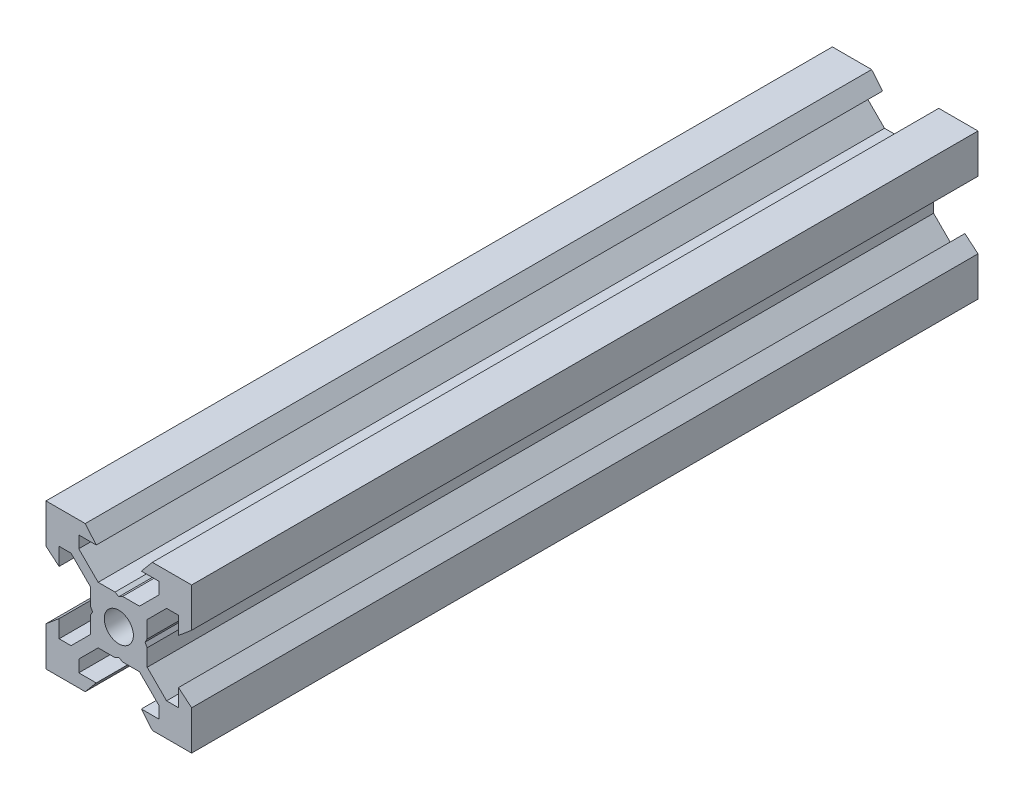
SolidWorks part; units mm, degrees
ref_plane "Front Plane" through (0, 0, 0) normal (0, 0, 1) x (1, 0, 0)
ref_plane "Top Plane" through (0, 0, 0) normal (0, 1, 0) x (1, 0, 0)
ref_plane "Right Plane" through (0, 0, 0) normal (1, 0, 0) x (0, 0, -1)
sketch "Sketch1" plane through (0, 0, 0) normal (0, 0, 1) x (1, 0, 0)
  line L0 (10, 10) -> (4.6104, 10) construction
  line L1 (10, 10) -> (10, 4.6104) construction
  line L2 (10, -10) -> (10, -4.6104) construction
  line L3 (10, -10) -> (4.6104, -10) construction
  line L4 (10, 10) -> (10, 4.6104)
  line L5 (6.5607, 5.5) -> (8.2, 5.5)
  line L6 (5.5, 8.2) -> (5.5, 6.5607)
  line L7 (10, 10) -> (4.6104, 10)
  line L8 (10, 10) -> (10, 4.6104)
  line L9 (6.5607, 5.5) -> (3.9, 2.8393)
  line L10 (5.5, 6.5607) -> (2.8393, 3.9)
  line L11 (10, 4.6104) -> (8.2, 3.1)
  line L12 (4.6104, 10) -> (3.1, 8.2)
  line L13 (8.2, 3.1) -> (8.2, 5.5)
  line L14 (3.1, 8.2) -> (5.5, 8.2)
  line L15 (-6.5607, 5.5) -> (-8.2, 5.5)
  line L16 (6.5607, -5.5) -> (8.2, -5.5)
  line L17 (3.1, -8.2) -> (5.5, -8.2)
  line L18 (8.2, -3.1) -> (8.2, -5.5)
  line L19 (4.6104, -10) -> (3.1, -8.2)
  line L20 (10, -4.6104) -> (8.2, -3.1)
  line L21 (0.5196, -3.9) -> (0, -3.6)
  line L22 (0.5196, 3.9) -> (0, 3.6)
  line L23 (3.6, 0) -> (3.9, -0.5196)
  line L24 (3.9, 0.5196) -> (3.6, 0)
  line L25 (3.9, 0.5196) -> (3.9, 2.8393)
  line L26 (2.8393, 3.9) -> (0.5196, 3.9)
  line L27 (3.9, -2.8393) -> (3.9, -0.5196)
  line L28 (2.8393, -3.9) -> (0.5196, -3.9)
  line L29 (5.5, -6.5607) -> (2.8393, -3.9)
  line L30 (6.5607, -5.5) -> (3.9, -2.8393)
  line L31 (10, -10) -> (10, -4.6104)
  line L32 (10, -10) -> (4.6104, -10)
  line L33 (5.5, -8.2) -> (5.5, -6.5607)
  line L34 (-6.5607, -5.5) -> (-8.2, -5.5)
  line L35 (10, -10) -> (10, -4.6104)
  line L36 (0, 0) -> (0, 8.2) construction
  line L37 (-10, -10) -> (-4.6104, -10) construction
  line L38 (-10, -10) -> (-10, -4.6104) construction
  line L39 (-10, 10) -> (-10, 4.6104) construction
  line L40 (-10, 10) -> (-4.6104, 10) construction
  line L41 (-10, -10) -> (-10, -4.6104)
  line L43 (-5.5, -8.2) -> (-5.5, -6.5607)
  line L44 (-10, -10) -> (-4.6104, -10)
  line L45 (-10, -10) -> (-10, -4.6104)
  line L46 (-6.5607, -5.5) -> (-3.9, -2.8393)
  line L47 (-5.5, -6.5607) -> (-2.8393, -3.9)
  line L48 (-2.8393, -3.9) -> (-0.5196, -3.9)
  line L49 (-3.9, -2.8393) -> (-3.9, -0.5196)
  line L50 (-2.8393, 3.9) -> (-0.5196, 3.9)
  line L51 (-3.9, 0.5196) -> (-3.9, 2.8393)
  line L52 (-3.9, 0.5196) -> (-3.6, 0)
  line L53 (-3.6, 0) -> (-3.9, -0.5196)
  line L54 (-0.5196, 3.9) -> (0, 3.6)
  line L55 (-0.5196, -3.9) -> (0, -3.6)
  line L56 (-10, -4.6104) -> (-8.2, -3.1)
  line L57 (-4.6104, -10) -> (-3.1, -8.2)
  line L58 (-8.2, -3.1) -> (-8.2, -5.5)
  line L59 (-3.1, -8.2) -> (-5.5, -8.2)
  line L60 (-10, -10) -> (10, -10) construction
  line L61 (-10, -10) -> (-10, 10) construction
  line L62 (-3.1, 8.2) -> (-5.5, 8.2)
  line L63 (-8.2, 3.1) -> (-8.2, 5.5)
  line L64 (-4.6104, 10) -> (-3.1, 8.2)
  line L65 (-10, 4.6104) -> (-8.2, 3.1)
  line L66 (-5.5, 6.5607) -> (-2.8393, 3.9)
  line L67 (-6.5607, 5.5) -> (-3.9, 2.8393)
  line L68 (-10, 10) -> (-10, 4.6104)
  line L69 (-10, 10) -> (-4.6104, 10)
  line L70 (-5.5, 8.2) -> (-5.5, 6.5607)
  line L71 (-10, 10) -> (10, 10) construction
  line L72 (-10, 10) -> (-10, 4.6104)
  line L73 (10, -10) -> (10, 10) construction
  line L74 (-10, -10) -> (10, 10) construction
  line L75 (-10, 10) -> (10, -10) construction
  circle A0 centre (0, 0) radius 2
  dimension "D7" = 4
  dimension "D1" = 20
  dimension "D2" = 5.3896
  dimension "D3" = 4.5
  dimension "D4" = 50
  dimension "D5" = 1.8
  dimension "D6" = 1.5104
  dimension "D8" = 5.5
  dimension "D9" = 120
  dimension "D10" = 0.3
  dimension "D11" = 2.3197
  dimension "D12" = 7.8
  dimension "D13" = 7.8
  dimension "D14" = 1.5
  dimension "D15" = 2.6607
extrude "Boss-Extrude1" add sketch "Sketch1" along normal mid plane 108 contours L70 L62 L64 L69 L68 L65 L63 L15 L67 L51 L52 L53 L49 L46 L34 L58 L56 L41 L44 L57 L59 L43 L47 L48 L55 L21 L28 L29 L33 L17 L19 L32 L31 L20 L18 L16 L30 L27 L23 L24 L25 L9 L5 L13 L11 L4 L7 L12 L14 L6 L10
